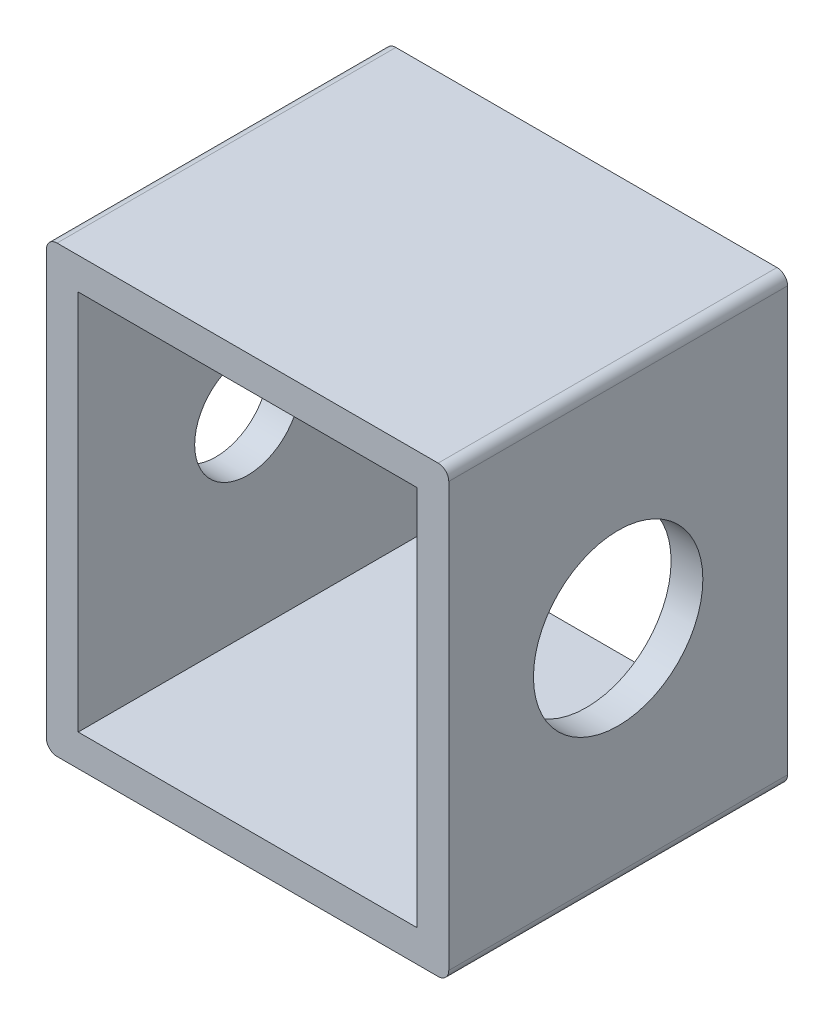
SolidWorks part; units mm, degrees
material "1.0545 (S355N)"
ref_plane "Płaszczyzna XY" through (0, 0, 0) normal (0, 0, 1) x (1, 0, 0)
ref_plane "Płaszczyzna XZ" through (0, 0, 0) normal (0, 1, 0) x (1, 0, 0)
ref_plane "Płaszczyzna YZ" through (0, 0, 0) normal (1, 0, 0) x (0, 0, -1)
sketch "Szkic1" plane through (0, 0, 0) normal (0, 0, 1) x (1, 0, 0)
  line L0 (0.5, 0) -> (18.5, 0)
  line L1 (19, 0.5) -> (19, 20.5)
  line L2 (18.5, 21) -> (0.5, 21)
  line L3 (0, 20.5) -> (0, 0.5)
  arc A0 (18.5, 0) -> (19, 0.5) centre (18.5, 0.5) ccw
  arc A1 (0.5, 0) -> (0, 0.5) centre (0.5, 0.5) cw
  arc A2 (0.5, 21) -> (0, 20.5) centre (0.5, 20.5) ccw
  arc A3 (19, 20.5) -> (18.5, 21) centre (18.5, 20.5) ccw
  point P7 (19, 0)
  point P10 (0, 0)
  point P13 (0, 21)
  dimension "D3" = 0.5
  dimension "D1" = 19
  dimension "D2" = 21
extrude "Dodanie-wyciągnięcie1" add sketch "Szkic1" along normal blind 16
shell "Skorupa1" thickness 1.5
sketch "Szkic12" plane through (0, 0, 0) normal (-1, 0, 0) x (0, 0, 1)
  circle A0 centre (8, 10.5) radius 2.5
extrude "Wytnij-wyciągnięcie2" cut sketch "Szkic12" against normal up to next
sketch "Szkic13" plane through (19, 0, 0) normal (1, 0, 0) x (0, 0, -1)
  circle A0 centre (-8, 10.5) radius 4
extrude "Wytnij-wyciągnięcie3" cut sketch "Szkic13" against normal up to next
